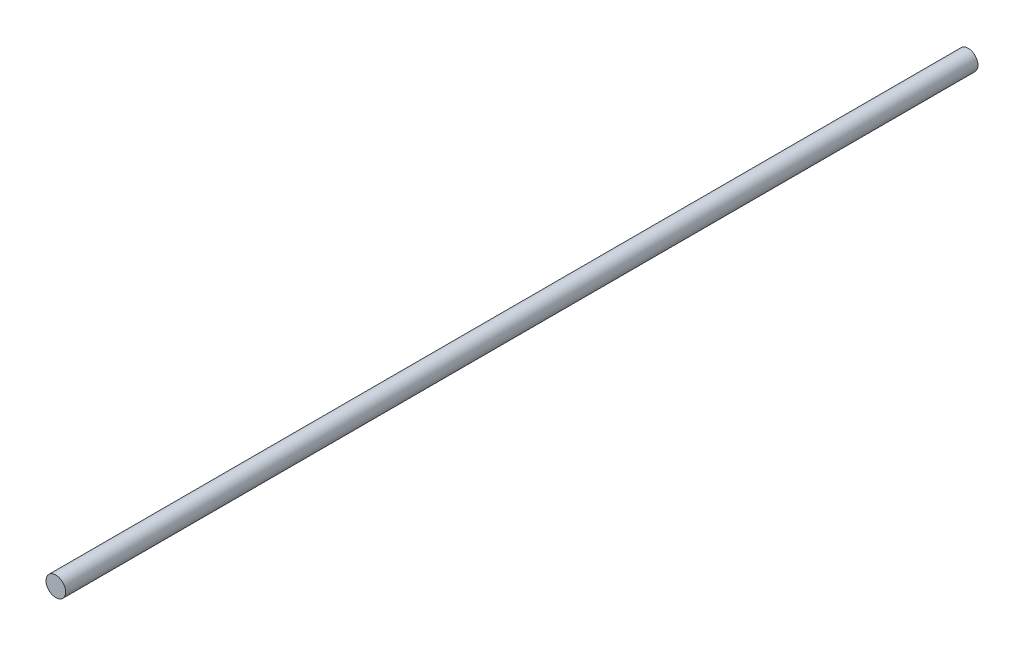
SolidWorks part; units mm, degrees
ref_plane "Front Plane" through (0, 0, 0) normal (0, 0, 1) x (1, 0, 0)
ref_plane "Top Plane" through (0, 0, 0) normal (0, 1, 0) x (1, 0, 0)
ref_plane "Right Plane" through (0, 0, 0) normal (1, 0, 0) x (0, 0, -1)
sketch "Sketch1" plane through (0, 0, 0) normal (0, 0, 1) x (1, 0, 0)
  circle A0 centre (0, 0) radius 3.9688
  dimension "D1" = 7.9375
extrude "Boss-Extrude1" add sketch "Sketch1" along normal blind 368.3
